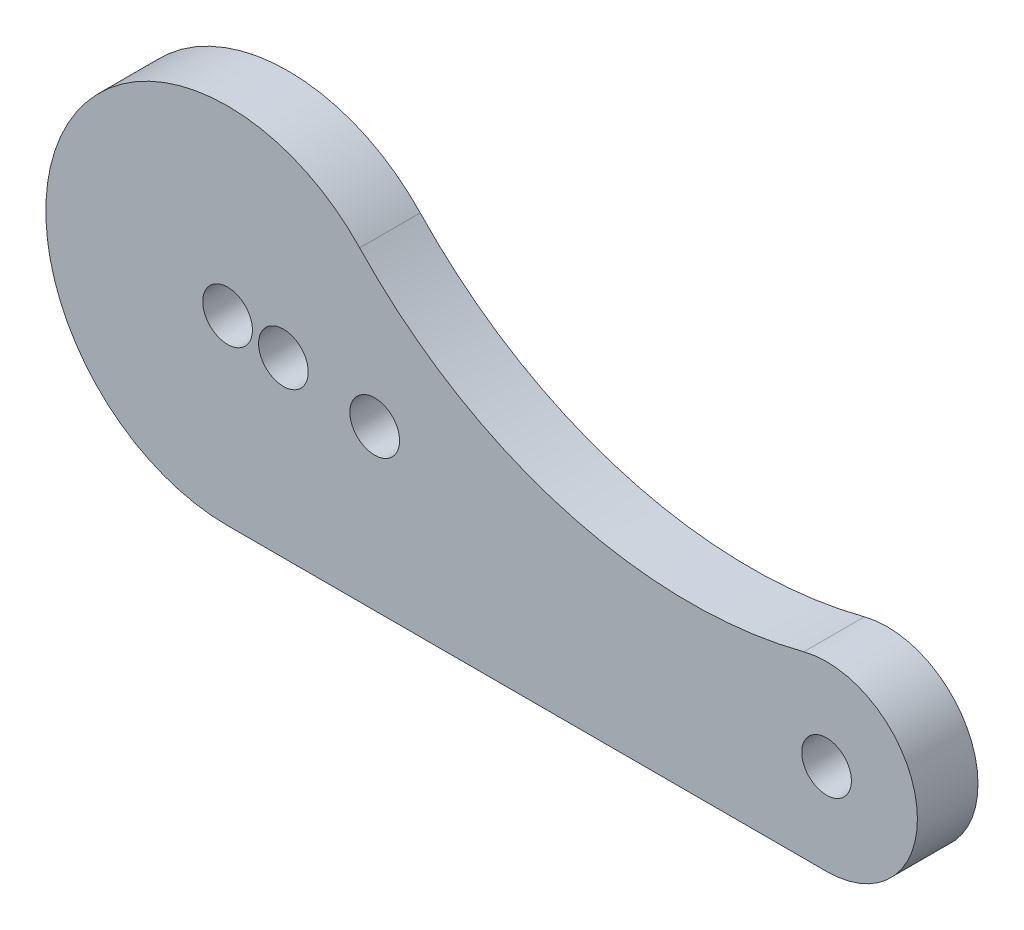
SolidWorks part; units mm, degrees
material "Acrílico (Impacto medio-alto)"
ref_plane "Piano frontale" through (0, 0, 0) normal (0, 0, 1) x (1, 0, 0)
ref_plane "Piano superiore" through (0, 0, 0) normal (0, 1, 0) x (1, 0, 0)
ref_plane "Piano destro" through (0, 0, 0) normal (1, 0, 0) x (0, 0, -1)
sketch "Schizzo1" plane through (0, 0, 0) normal (0, 0, 1) x (1, 0, 0)
  line L0 (0, -15) -> (49.4343, -15)
  circle A0 centre (0, 0) radius 2.05
  circle A1 centre (49.4343, -7.5) radius 2.05
  arc A2 (10.901, 10.3038) -> (0, -15) centre (0, 0) ccw
  arc A3 (49.4343, -15) -> (47.5542, -0.2395) centre (49.4343, -7.5) ccw
  arc A4 (10.901, 10.3038) -> (47.5542, -0.2395) centre (38.1536, 36.0631) ccw
  dimension "D1" = 4.1
  dimension "D4" = 30
  dimension "D5" = 15
  dimension "D6" = 75
  dimension "D3" = 50
extrude "Estrusione-Estrusione1" add sketch "Schizzo1" along normal blind 5
sketch "Sketch1" plane through (0, 0, 5) normal (0, 0, 1) x (1, 0, 0)
  line L0 (14.0254, -2.1279) -> (12.142, -1.8421) construction
  line L1 (12.142, -1.8421) -> (10.2585, -1.5564) construction
  line L2 (10.2585, -1.5564) -> (8.3751, -1.2706) construction
  line L3 (8.3751, -1.2706) -> (6.4916, -0.9849) construction
  line L4 (6.4916, -0.9849) -> (4.6082, -0.6991) construction
  line L5 (4.6082, -0.6991) -> (0, 0) construction
  circle A0 centre (4.6082, -0.6991) radius 2.05
  circle A1 centre (12.142, -1.8421) radius 2.05
  point P11 (49.4343, -7.5)
  dimension "D1" = 4.1
  dimension "D2" = 4.1
  dimension "D3" = 1.905
  dimension "D4" = 4.6609
extrude "Cut-Extrude1" cut sketch "Sketch1" against normal up to next
